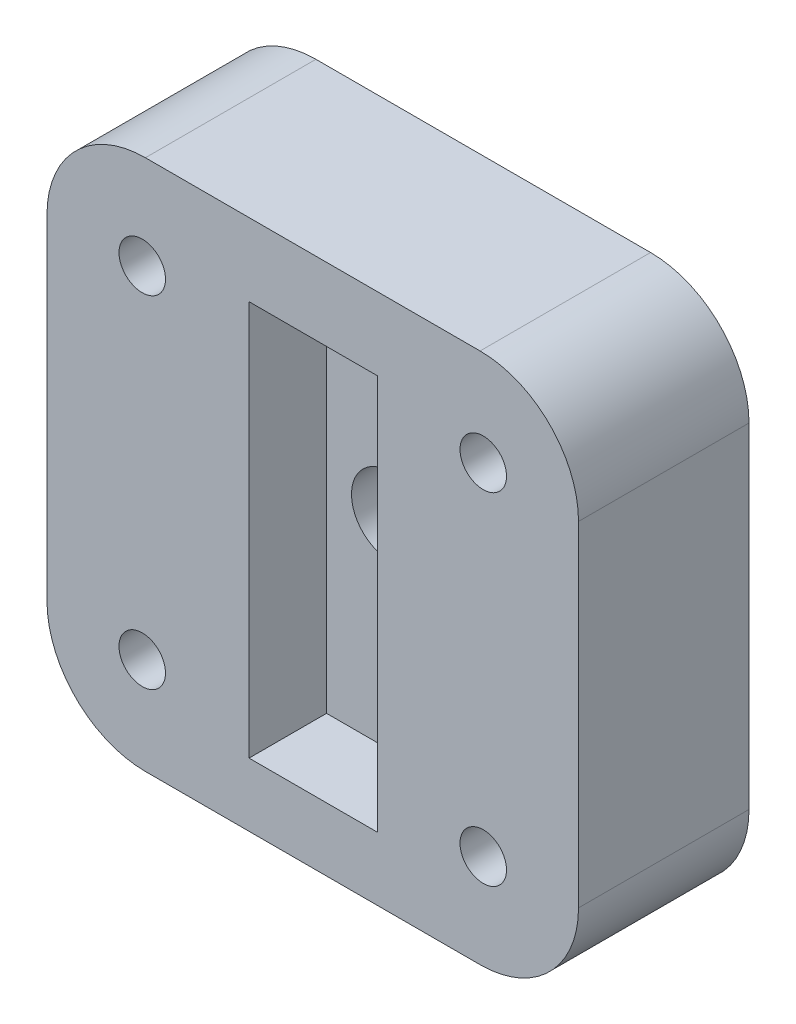
SolidWorks part; units mm, degrees
ref_plane "Front Plane" through (0, 0, 0) normal (0, 0, 1) x (1, 0, 0)
ref_plane "Top Plane" through (0, 0, 0) normal (0, 1, 0) x (1, 0, 0)
ref_plane "Right Plane" through (0, 0, 0) normal (1, 0, 0) x (0, 0, -1)
sketch "Sketch1" plane through (0, 0, 0) normal (0, 0, 1) x (1, 0, 0)
  line L1 (11, -11) -> (-11, -11)
  line L2 (11, -11) -> (11, 11)
  line L3 (11, 11) -> (-11, 11)
  line L4 (-11, -11) -> (-11, 11)
  line L5 (11, -11) -> (-11, 11) construction
  line L6 (11, 11) -> (-11, -11) construction
  line L7 (-17.145, 17.145) -> (17.145, 17.145)
  line L8 (-17.145, 17.145) -> (-17.145, -17.145)
  line L9 (-17.145, -17.145) -> (17.145, -17.145)
  line L10 (17.145, 17.145) -> (17.145, -17.145)
  line L11 (-17.145, 17.145) -> (17.145, -17.145) construction
  line L12 (-17.145, -17.145) -> (17.145, 17.145) construction
  circle A0 centre (-11, 11) radius 1.5
  circle A1 centre (11, 11) radius 1.5
  circle A2 centre (-11, -11) radius 1.5
  circle A3 centre (11, -11) radius 1.5
  point P0 (0, 0)
  point P10 (0, 0)
  dimension "D3" = 3
  dimension "D4" = 3
  dimension "D5" = 3
  dimension "D6" = 3
  dimension "D1" = 22
  dimension "D2" = 22
  dimension "D7" = 34.29
  dimension "D8" = 34.29
extrude "Boss-Extrude1" add sketch "Sketch1" along normal blind 11 contours L10 L7 L8 L9 A3 L1 A2 L4 A0 L3 A1 L2 | A3 L2 A1 L3 A0 L4 A2 L1
sketch "Sketch2" plane through (0, 0, 11) normal (0, 0, 1) x (1, 0, 0)
  line L5 (17.145, 17.145) -> (17.145, -17.145) construction
  line L7 (-4.109, 12.446) -> (4.191, 12.446)
  line L8 (-4.109, 12.446) -> (-4.109, -13.054)
  line L9 (-4.109, -13.054) -> (4.191, -13.054)
  line L10 (4.191, 12.446) -> (4.191, -13.054)
  line L11 (-17.145, 17.145) -> (17.145, 17.145) construction
  dimension "D1" = 8.3
  dimension "D2" = 25.5
  dimension "D3" = 12.954
  dimension "D4" = 4.699
extrude "Cut-Extrude1" cut sketch "Sketch2" against normal blind 5
sketch "Sketch3" plane through (0, 0, 6) normal (0, 0, 1) x (1, 0, 0)
  circle A0 centre (0, 0) radius 2.5
  dimension "D1" = 5
extrude "Cut-Extrude2" cut sketch "Sketch3" against normal blind 5
sketch "Sketch5" plane through (0, 0, 0) normal (0, 0, -1) x (-1, 0, 0)
  circle A0 centre (0, 0) radius 4.15
  dimension "D1" = 8.3
extrude "Cut-Extrude4" cut sketch "Sketch5" against normal blind 3
fillet "Fillet2" radius 6.35 4 edges at (17.145, -17.145, 5.5) (-17.145, -17.145, 5.5) (17.145, 17.145, 5.5) (-17.145, 17.145, 5.5)
